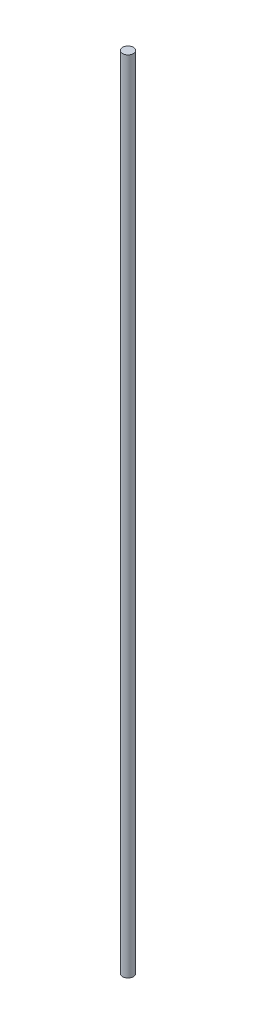
SolidWorks part; units mm, degrees
material "Hexcel AS4C (3000 Filaments)"
ref_plane "Front Plane" through (0, 0, 0) normal (0, 0, 1) x (1, 0, 0)
ref_plane "Top Plane" through (0, 0, 0) normal (0, 1, 0) x (1, 0, 0)
ref_plane "Right Plane" through (0, 0, 0) normal (1, 0, 0) x (0, 0, -1)
sketch "Sketch1" plane through (0, 0, 0) normal (0, 1, 0) x (1, 0, 0)
  circle A0 centre (0, 0) radius 1
  dimension "D1" = 2
extrude "Boss-Extrude1" add sketch "Sketch1" along normal mid plane 147
